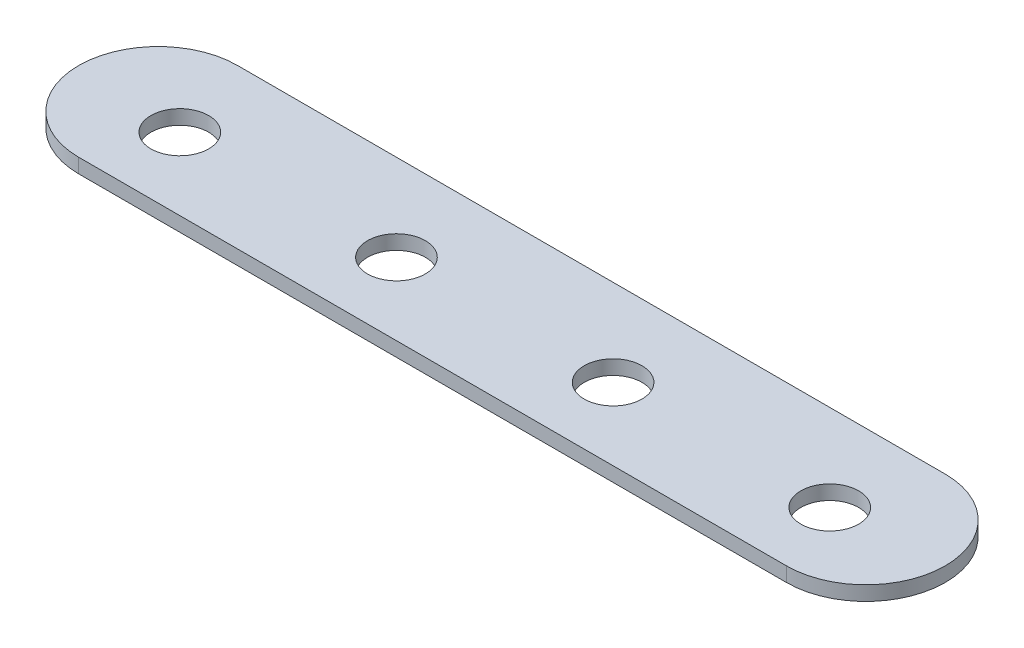
SolidWorks part; units mm, degrees
ref_plane "Front Plane" through (0, 0, 0) normal (0, 0, 1) x (1, 0, 0)
ref_plane "Top Plane" through (0, 0, 0) normal (0, 1, 0) x (1, 0, 0)
ref_plane "Right Plane" through (0, 0, 0) normal (1, 0, 0) x (0, 0, -1)
sketch "Sketch1" plane through (0, 0, 0) normal (0, 1, 0) x (1, 0, 0)
  line L1 (-5.5, 0) -> (-54.5, 0)
  line L3 (-5.5, 11) -> (-54.5, 11)
  circle A0 centre (-52.5, 5) radius 2
  circle A1 centre (-37.5, 5) radius 2
  circle A2 centre (-22.5, 5) radius 2
  circle A3 centre (-7.5, 5) radius 2
  arc A4 (-54.5, 11) -> (-54.5, 0) centre (-54.5, 5.5) ccw
  arc A5 (-5.5, 0) -> (-5.5, 11) centre (-5.5, 5.5) ccw
  dimension "D4" = 15
  dimension "D5" = 15
  dimension "D6" = 15
extrude "Boss-Extrude1" add sketch "Sketch1" along normal blind 1
